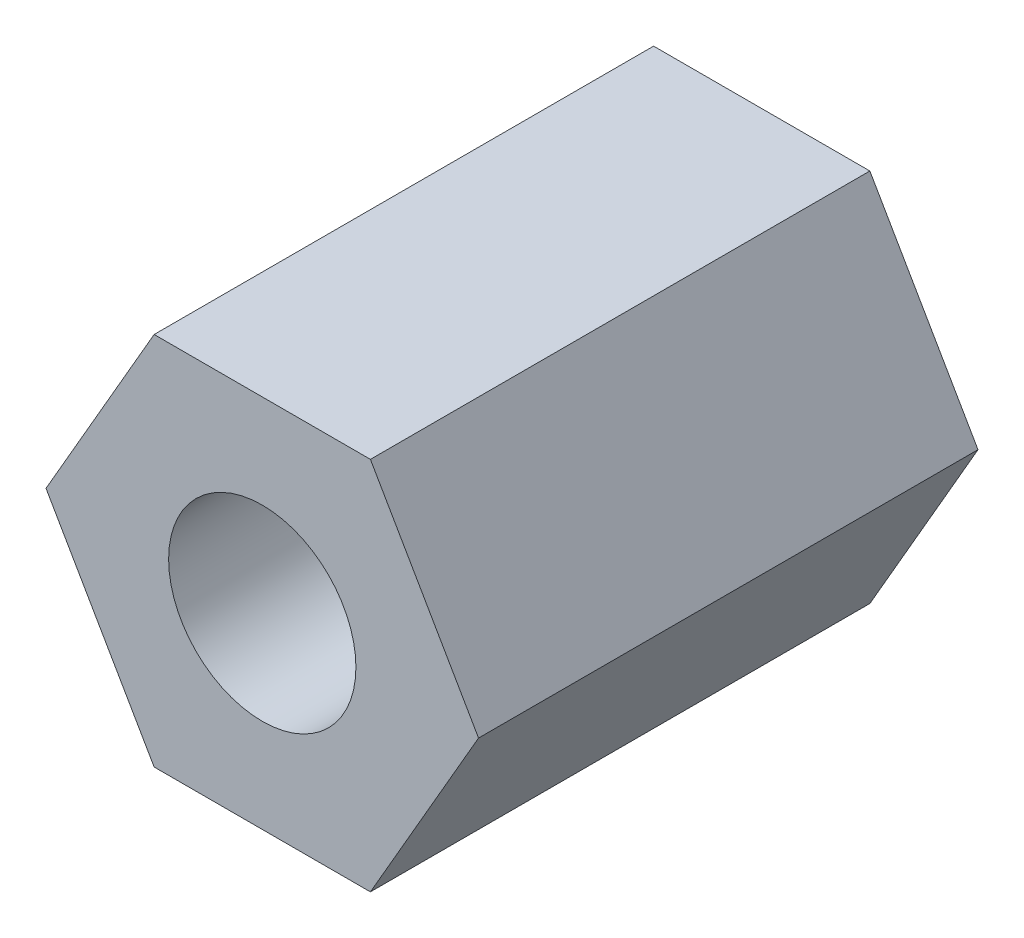
SolidWorks part; units mm, degrees
ref_plane "前视基准面" through (0, 0, 0) normal (0, 0, 1) x (1, 0, 0)
ref_plane "上视基准面" through (0, 0, 0) normal (0, 1, 0) x (1, 0, 0)
ref_plane "右视基准面" through (0, 0, 0) normal (1, 0, 0) x (0, 0, -1)
sketch "草图1" plane through (0, 0, 0) normal (0, 0, 1) x (1, 0, 0)
  line L1 (1.7321, 3) -> (-1.7321, 3)
  line L2 (-1.7321, 3) -> (-3.4641, 0)
  line L3 (-3.4641, 0) -> (-1.7321, -3)
  line L4 (-1.7321, -3) -> (1.7321, -3)
  line L5 (1.7321, -3) -> (3.4641, 0)
  line L6 (3.4641, 0) -> (1.7321, 3)
  circle A0 centre (0, 0) radius 3 construction
  circle A1 centre (0, 0) radius 1.5
  dimension "D1" = 6
  dimension "D2" = 3
extrude "凸台-拉伸1" add sketch "草图1" along normal blind 8
